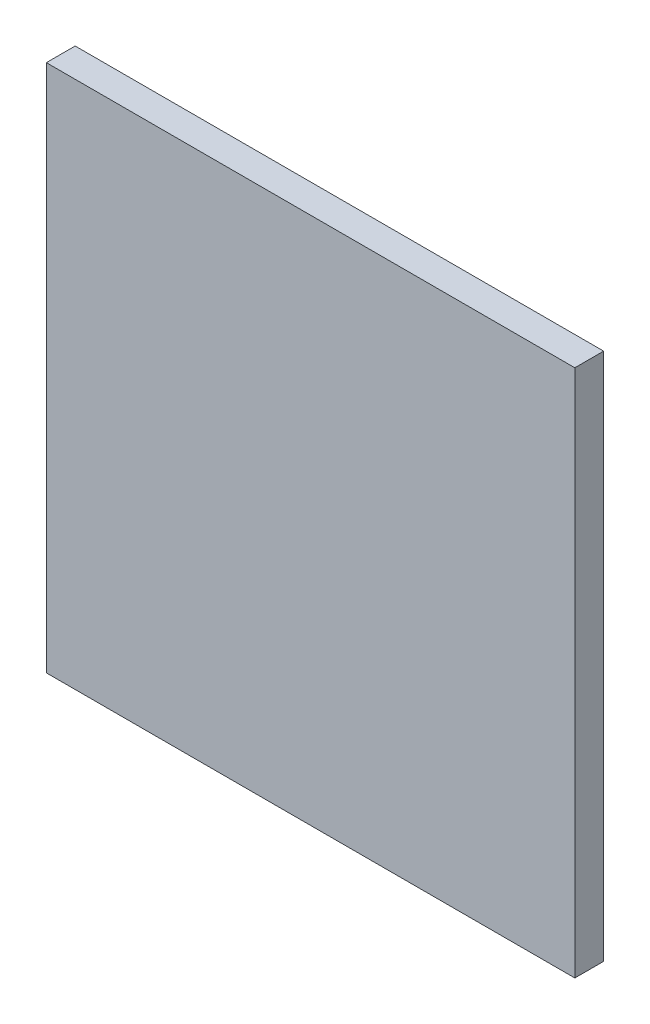
SolidWorks part; units mm, degrees
ref_plane "Plan de face" through (0, 0, 0) normal (0, 0, 1) x (1, 0, 0)
ref_plane "Plan de dessus" through (0, 0, 0) normal (0, 1, 0) x (1, 0, 0)
ref_plane "Plan de droite" through (0, 0, 0) normal (1, 0, 0) x (0, 0, -1)
sketch "Esquisse1" plane through (0, 0, 0) normal (0, 0, 1) x (1, 0, 0)
  line L1 (-27.5, -27.5) -> (27.5, -27.5)
  line L2 (-27.5, -27.5) -> (-27.5, 27.5)
  line L3 (-27.5, 27.5) -> (27.5, 27.5)
  line L4 (27.5, -27.5) -> (27.5, 27.5)
  dimension "D1" = 55
  dimension "D2" = 55
  dimension "D3" = 27.5
  dimension "D4" = 27.5
extrude "Boss.-Extru.1" add sketch "Esquisse1" along normal blind 3
